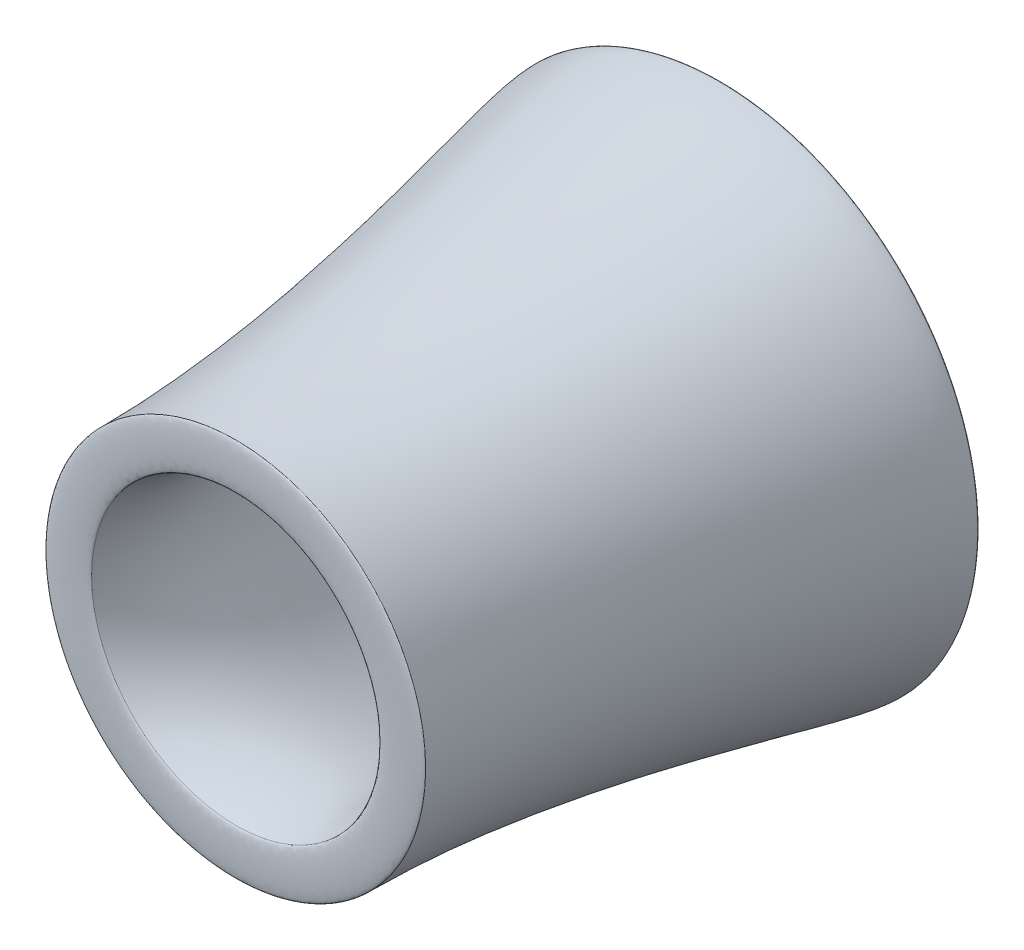
SolidWorks part; units mm, degrees
ref_plane "Front Plane" through (0, 0, 0) normal (0, 0, 1) x (1, 0, 0)
ref_plane "Top Plane" through (0, 0, 0) normal (0, 1, 0) x (1, 0, 0)
ref_plane "Right Plane" through (0, 0, 0) normal (1, 0, 0) x (0, 0, -1)
sketch "Sketch1" plane through (0, 0, 0) normal (0, 0, 1) x (1, 0, 0)
  circle A0 centre (0, 0) radius 50.8
  dimension "D1" = 101.6
ref_plane "Plane1" through (0, -254, 0) normal (0, 1, 0) x (1, 0, 0)
sketch "Sketch6" plane through (0, 0, 0) normal (0, 1, 0) x (1, 0, 0)
  line L0 (0, -99.6848) -> (0, 145.6048) construction
ref_plane "Plane2" through (0, -114.3, 0) normal (0, 1, 0) x (1, 0, 0)
sketch "Sketch12" plane through (0, 0, 0) normal (0, 1, 0) x (1, 0, 0)
  line L0 (0, -1104.7568) -> (0, -908.6135) construction
ref_plane "Plane3" through (0, 0, 203.2) normal (0, 0, 1) x (1, 0, 0)
ref_plane "Plane4" through (0, 0, 889) normal (0, 0, 1) x (1, 0, 0)
sketch "Sketch17" plane through (0, 0, 0) normal (0, 1, 0) x (1, 0, 0)
  line L0 (-259.4955, -43.5301) -> (-259.4955, 70.1436) construction
  line L1 (-110.6437, -1316.1124) -> (-110.6437, -853.5386) construction
  line L2 (-259.4955, 45.4622) -> (-387.328, 45.4622)
  line L3 (-387.328, 45.4622) -> (-387.328, -1084.8928)
  line L4 (-387.328, -1084.8928) -> (-110.6437, -1084.8928)
  spline S0 degree 3 poles (-259.4955, 45.4622) (-259.4955, -7.1736) (-207.7477, -105.8122) (-173.3147, -383.1384) (-92.4228, -818.9689) (-110.6437, -795.7842) (-110.6437, -1084.8928) knots 0 0 0 0 0.158009 0.206507 0.484977 1 1 1 1
sketch "Sketch21" plane through (0, 0, 0) normal (0, 1, 0) x (1, 0, 0)
  line L0 (-871.5641, -22.8536) -> (-871.5641, 113.778) construction
  line L1 (-639.3342, -1315.9117) -> (-639.3342, -853.874) construction
  line L2 (-710.4538, 376.2263) -> (-871.5641, 376.2263) construction
  line L3 (-486.2776, -1251.9958) -> (-639.3342, -1251.9958) construction
  line L4 (-486.2776, -1251.9958) -> (-639.3342, -1251.9958)
  line L6 (-710.4538, 376.2263) -> (-871.5641, 376.2263)
  spline S0 degree 3 poles (-710.4538, 376.2263) (-720.0219, 125.2128) (-670.557, -438.7246) (-344.1325, -890.1844) (-486.2776, -1251.9958) knots 0 0 0 0 0.206507 1 1 1 1
  spline S1 degree 3 poles (-871.5641, 376.2263) (-871.5641, 250.8424) (-639.3342, -521.6867) (-639.3342, -1251.9958) knots 0 0 0 0 1 1 1 1
  point P10 (-492.6763, 33.3566)
  point P11 (-415.319, 23.7629)
  point P12 (0, 0)
  point P13 (-280.19, -218.5963)
  point P14 (-107.7203, -744.3436)
  point P15 (-227.4717, -631.3121)
  point P16 (-359.5981, -196.0862)
  point P17 (-490.3965, 111.2419)
  point P18 (-225.5389, -544.3498)
  point P19 (0, 0)
  point P20 (-320.3524, -188.2581)
  point P21 (-1266.1516, -1124.0755)
  point P22 (-1622.7508, 71.1679)
  point P23 (-1359.7117, 323.9343)
  point P24 (-1266.1516, 0)
  point P25 (-1152.7202, -633.8849)
  point P26 (-1126.7483, -1165.0291)
  point P27 (-1262.211, -558.2651)
  point P28 (-1331.4417, 0)
  point P29 (-1224.8431, -715.1836)
  point P30 (-1398.233, 56.6903)
  point P31 (0, 0)
  point P32 (-1398.1755, -167.5318)
  point P33 (-1266.1516, -584.9605)
  point P34 (-1223.5153, -859.5675)
  point P35 (-1203.2391, -922.5419)
  point P36 (-1348.3825, -217.9167)
  point P37 (-1266.1516, -596.9331)
  point P38 (-791.188, -1161.4097)
  point P39 (-937.1403, 331.0074)
  point P40 (-876.0162, -670.3844)
  point P41 (-935.205, -203.0464)
  point P42 (-1224.6694, 345.4636)
  point P43 (-935.205, -1217.3061)
  point P44 (0, 0)
  point P45 (0, 0)
  point P46 (0, 0)
  point P47 (-977.0405, -152.0983)
  point P48 (-340.1791, -1162.6263)
  point P49 (-639.3342, -1253.9543)
  point P50 (-575.8293, -461.0111)
  point P51 (-696.8594, -51.9544)
  point P52 (-710.4538, 314.66)
  point P53 (-871.5641, 376.2263)
  point P54 (-531.7615, -402.0232)
  point P55 (-559.1222, -531.669)
  point P56 (-486.2776, -1251.9958)
  point P57 (0, 0)
revolve "Revolve2" add sketch "Sketch21" angle 360 about L0
sketch "Sketch22" plane through (0, 0, 0) normal (0, 1, 0) x (1, 0, 0)
  line L0 (-871.5641, 376.2263) -> (-710.4538, 376.2263)
  line L1 (-710.4538, 372.4173) -> (-710.4538, 380.0354) construction
  line L2 (-871.5641, 377.6191) -> (-871.5641, 374.8336) construction
  spline S0 degree 3 poles (-871.5641, 376.2263) (-871.5641, 393.1597) (-710.4538, 393.1597) (-710.4538, 376.2263) knots 0 0 0 0 1 1 1 1
revolve "Revolve3" add sketch "Sketch22" angle 360 about L0
sketch "Sketch23" plane through (0, 0, 0) normal (0, 1, 0) x (1, 0, 0)
  line L0 (-639.3342, -1251.9958) -> (-486.2776, -1251.9958)
  line L1 (-639.3342, -1261.2068) -> (-639.3342, -1242.7847) construction
  line L2 (-486.2776, -1241.4228) -> (-486.2776, -1262.5688) construction
  spline S0 degree 3 poles (-639.3342, -1251.9958) (-639.3342, -1264.6958) (-486.2776, -1264.6958) (-486.2776, -1251.9958) knots 0 0 0 0 1 1 1 1
revolve "Revolve4" add sketch "Sketch23" angle 360 about L0
